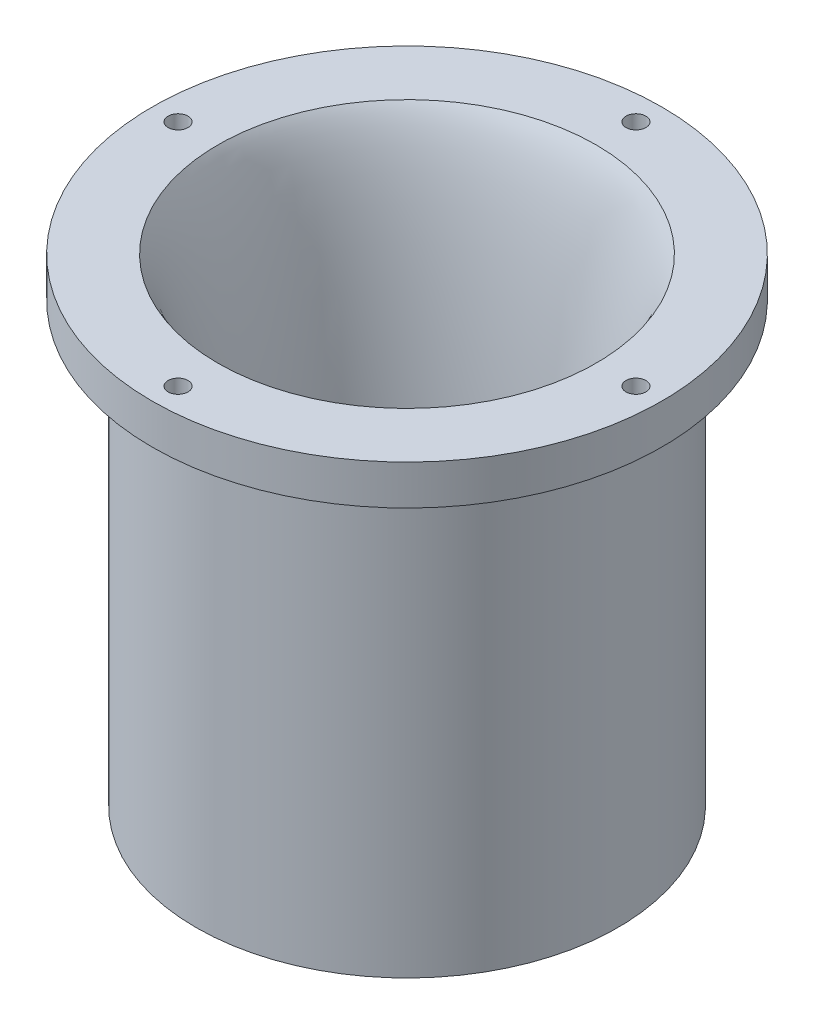
SolidWorks part; units mm, degrees
material "PE High Density"
ref_plane "Front Plane" through (0, 0, 0) normal (0, 0, 1) x (1, 0, 0)
ref_plane "Top Plane" through (0, 0, 0) normal (0, 1, 0) x (1, 0, 0)
ref_plane "Right Plane" through (0, 0, 0) normal (1, 0, 0) x (0, 0, -1)
sketch "Sketch1" plane through (0, 0, 0) normal (1, 0, 0) x (0, 0, -1)
  line L0 (38, 0) -> (38, -20)
  line L1 (35, 0) -> (38, 0)
  line L6 (0, 0) -> (0, 37.2702)
  line L14 (0, 37.2702) -> (0, 66.6796)
  line L15 (47.5, 100) -> (0, 100)
  line L17 (38, -20) -> (53, -20)
  line L18 (64, 100) -> (64, 90)
  line L19 (64, 100) -> (47.5, 100)
  line L20 (64, 90) -> (56.6349, 90)
  line L21 (53, -20) -> (53, 90)
  line L22 (53, 90) -> (56.6349, 90)
  line L23 (35, 0) -> (0, 0)
  spline S0 degree 3 poles (35, 0) (35, 0.7435) (35.036, 3.6043) (34.5552, 30.1875) (38.4522, 87.1238) (47.5, 100) knots 0 0 0 0 0.040284 0.140284 1 1 1 1
  dimension "D1" = 38
  dimension "D5" = 100
  dimension "D2" = 16.5
  dimension "D3" = 3
  dimension "D4" = 47.5
revolve "Revolve2" add sketch "Sketch1" angle 360 about L6
sketch "Sketch3" plane through (0, 100, 0) normal (0, 1, 0) x (1, 0, 0)
  circle A0 centre (0, 57.5) radius 2.5
  circle A1 centre (57.5, 0) radius 2.5
  circle A2 centre (0, -57.5) radius 2.5
  circle A3 centre (-57.5, 0) radius 2.5
  point P13 (0, 0)
  dimension "D1" = 4
extrude "Cut-Extrude1" cut sketch "Sketch3" against normal blind 10
